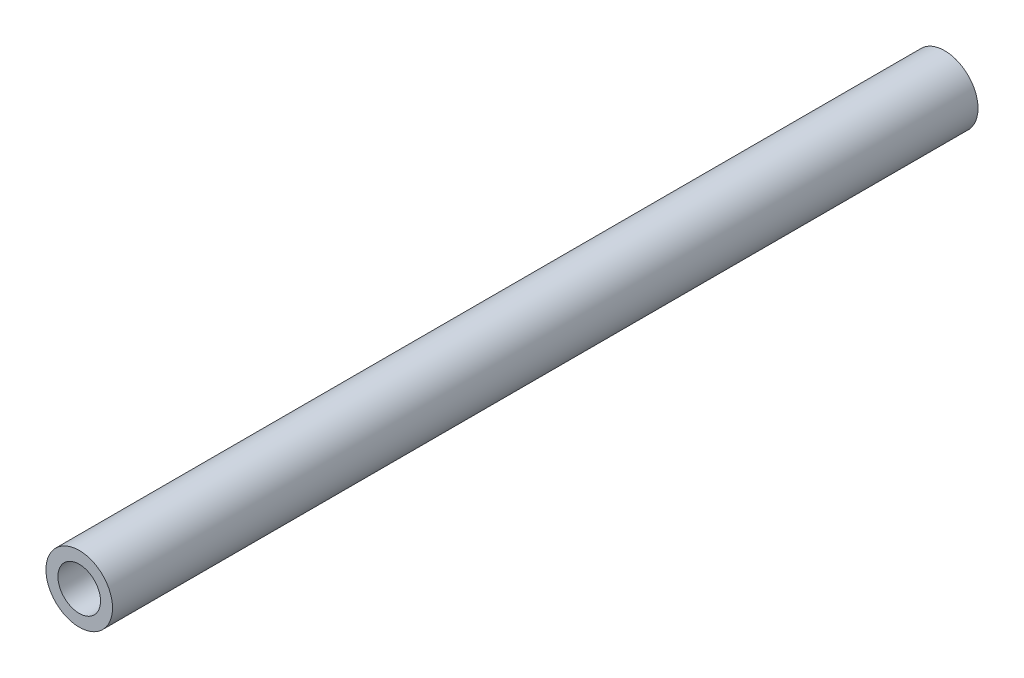
SolidWorks part; units mm, degrees
ref_plane "Front" through (0, 0, 0) normal (0, 0, 1) x (1, 0, 0)
ref_plane "Top" through (0, 0, 0) normal (0, 1, 0) x (1, 0, 0)
ref_plane "Right" through (0, 0, 0) normal (1, 0, 0) x (0, 0, -1)
sketch "Sketch1" plane through (0, 0, 0) normal (0, 0, 1) x (1, 0, 0)
  circle A0 centre (0, 0) radius 2.5
  circle A1 centre (0, 0) radius 1.6
extrude "Boss-Extrude2" add sketch "Sketch1" along normal blind 65
